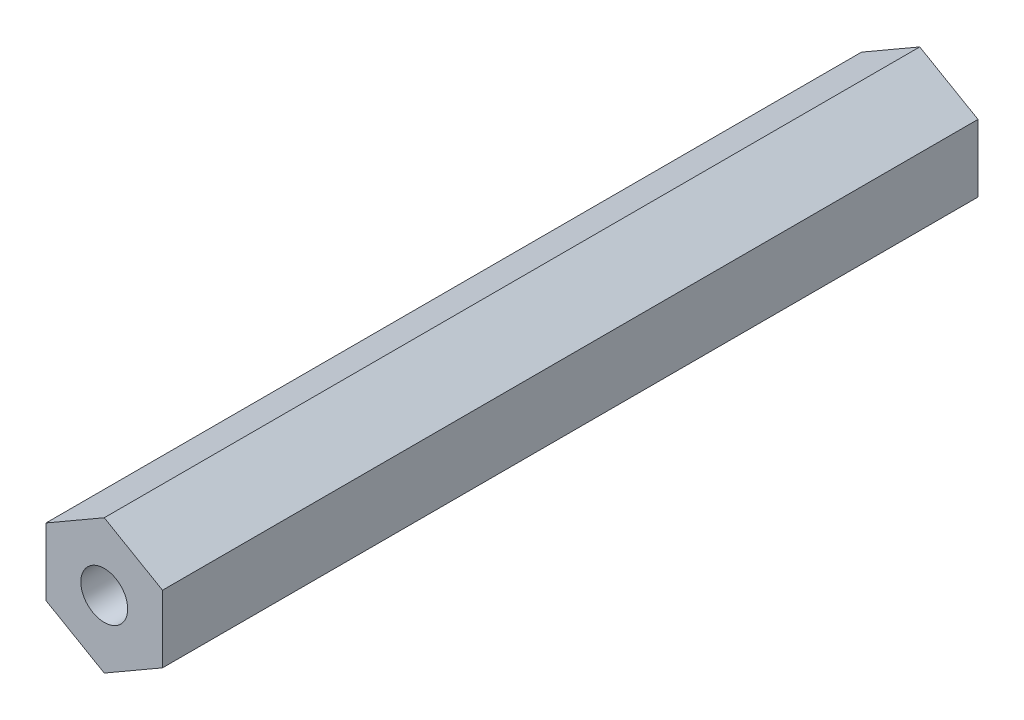
SolidWorks part; units mm, degrees
material "7075-T6 (SN)"
ref_plane "Front Plane" through (0, 0, 0) normal (0, 0, 1) x (1, 0, 0)
ref_plane "Top Plane" through (0, 0, 0) normal (0, 1, 0) x (1, 0, 0)
ref_plane "Right Plane" through (0, 0, 0) normal (1, 0, 0) x (0, 0, -1)
sketch "Sketch1" plane through (0, 0, 0) normal (0, 0, 1) x (1, 0, 0)
  line L1 (6.35, 3.6662) -> (0, 7.3323)
  line L2 (0, 7.3323) -> (-6.35, 3.6662)
  line L3 (-6.35, 3.6662) -> (-6.35, -3.6662)
  line L4 (-6.35, -3.6662) -> (0, -7.3323)
  line L5 (0, -7.3323) -> (6.35, -3.6662)
  line L6 (6.35, -3.6662) -> (6.35, 3.6662)
  circle A0 centre (0, 0) radius 6.35 construction
  dimension ".5" = 12.7
extrude "Boss-Extrude1" add sketch "Sketch1" along normal blind 88.9
hole_wizard "1/4-20 Tapped Hole1" positions "Sketch3" profile "Sketch4" tap size "1/4-20" standard "ANSI Inch"
sketch "Sketch3" plane through (0, 0, 88.9) normal (0, 0, 1) x (1, 0, 0)
  point P0 (0, 0)
sketch "Sketch4" plane through (0, 0, 88.9) normal (1, 0, 0) x (0, -1, 0)
  line L0 (0, 0) -> (0, 18.0438)
  line L1 (0, 18.0438) -> (2.5527, 16.51)
  line L2 (2.5527, 16.51) -> (2.5527, 0)
  line L5 (2.5527, 0) -> (0, 0)
  line L10 (0, 18.0438) -> (-2.5527, 16.51) construction
  line L11 (0, -6.35) -> (0, 107.95) construction
  dimension "Tap Drill Dia." = 5.1054
  dimension "Tap Drill Depth" = 16.51
  dimension "Drill Angle" = 118
cosmetic thread "Hole Thread1" parameters "D1"=12.7, "D2"=6.35
hole_wizard "1/4-20 Tapped Hole2" positions "Sketch6" profile "Sketch5" tap size "1/4-20" standard "ANSI Inch"
sketch "Sketch6" plane through (0, 0, 0) normal (0, 0, -1) x (-1, 0, 0)
  point P0 (0, 0)
sketch "Sketch5" plane through (0, 0, 0) normal (1, 0, 0) x (0, 1, 0)
  line L0 (0, 0) -> (0, 18.0438)
  line L1 (0, 18.0438) -> (2.5527, 16.51)
  line L2 (2.5527, 16.51) -> (2.5527, 0)
  line L5 (2.5527, 0) -> (0, 0)
  line L10 (0, 18.0438) -> (-2.5527, 16.51) construction
  line L11 (0, -6.35) -> (0, 107.95) construction
  dimension "Tap Drill Dia." = 5.1054
  dimension "Tap Drill Depth" = 16.51
  dimension "Drill Angle" = 118
cosmetic thread "Hole Thread2" parameters "D1"=12.7, "D2"=6.35
